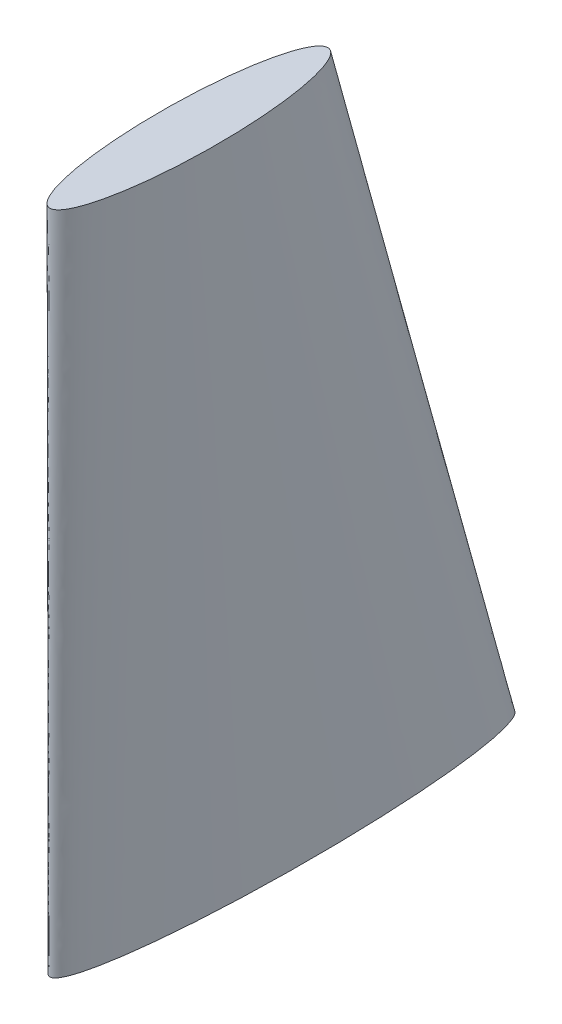
SolidWorks part; units mm, degrees
ref_plane "Front Plane" through (0, 0, 0) normal (0, 0, 1) x (1, 0, 0)
ref_plane "Top Plane" through (0, 0, 0) normal (0, 1, 0) x (1, 0, 0)
ref_plane "Right Plane" through (0, 0, 0) normal (1, 0, 0) x (0, 0, -1)
sketch "Sketch1" plane through (0, 0, 0) normal (0, 1, 0) x (1, 0, 0)
  line L0 (0, 122.5) -> (0, -122.5) construction
  ellipse E0 centre (0, 0) end of major axis (0, 122.5) minor radius 15
  dimension "D1" = 245
  dimension "D2" = 30
ref_plane "Plane1" through (0, 352, 0) normal (0, 1, 0) x (1, 0, 0)
sketch "Sketch2" plane through (0, 352, 0) normal (0, 1, 0) x (1, 0, 0)
  line L0 (0, 24.5) -> (0, -122.5) construction
  ellipse E0 centre (0, -49) end of major axis (0, -122.5) minor radius 15
  dimension "D1" = 147
  dimension "D2" = 30
loft "Loft1" add profiles "Sketch1", "Sketch2"
